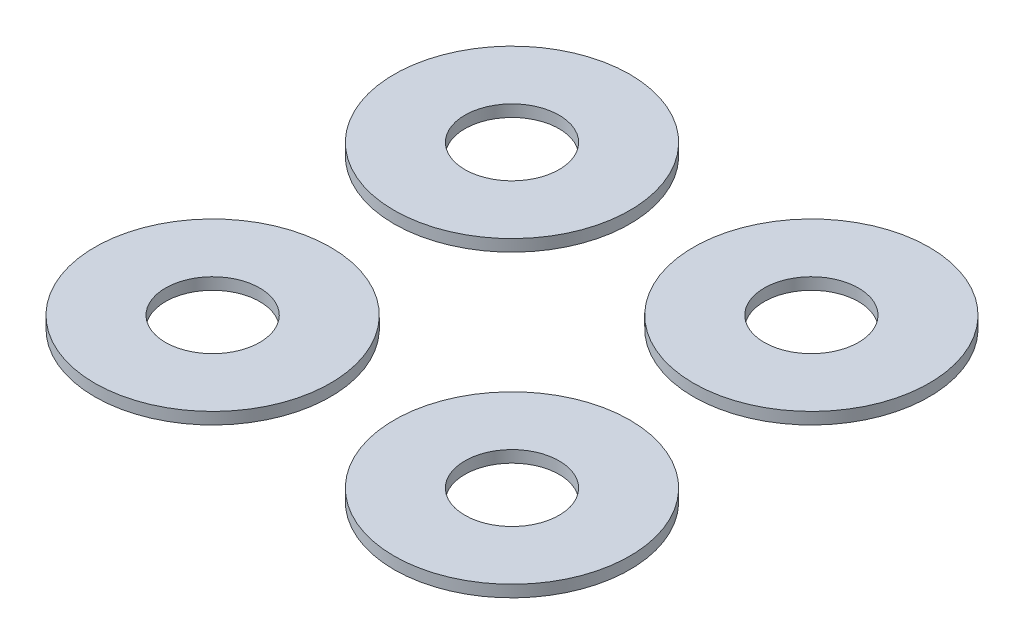
SolidWorks part; units mm, degrees
ref_plane "Front Plane" through (0, 0, 0) normal (0, 0, 1) x (1, 0, 0)
ref_plane "Top Plane" through (0, 0, 0) normal (0, 1, 0) x (1, 0, 0)
ref_plane "Right Plane" through (0, 0, 0) normal (1, 0, 0) x (0, 0, -1)
sketch "Sketch1" plane through (0, 0, 0) normal (0, 1, 0) x (1, 0, 0)
  line L1 (0, 0) -> (2.54, 0) construction
  line L2 (0, 0) -> (0, 2.54) construction
  line L3 (0, 2.54) -> (2.54, 2.54) construction
  line L4 (2.54, 0) -> (2.54, 2.54) construction
  circle A0 centre (0, 0) radius 0.4
  circle A1 centre (0, 0) radius 1
  circle A2 centre (0, 2.54) radius 0.4
  circle A3 centre (2.54, 2.54) radius 0.4
  circle A4 centre (2.54, 0) radius 0.4
  circle A5 centre (0, 2.54) radius 1
  circle A6 centre (2.54, 2.54) radius 1
  circle A7 centre (2.54, 0) radius 1
  dimension "D1" = 0.8
  dimension "D2" = 2
  dimension "D3" = 2.54
  dimension "D4" = 2.54
extrude "Boss-Extrude1" add sketch "Sketch1" along normal blind 0.1
